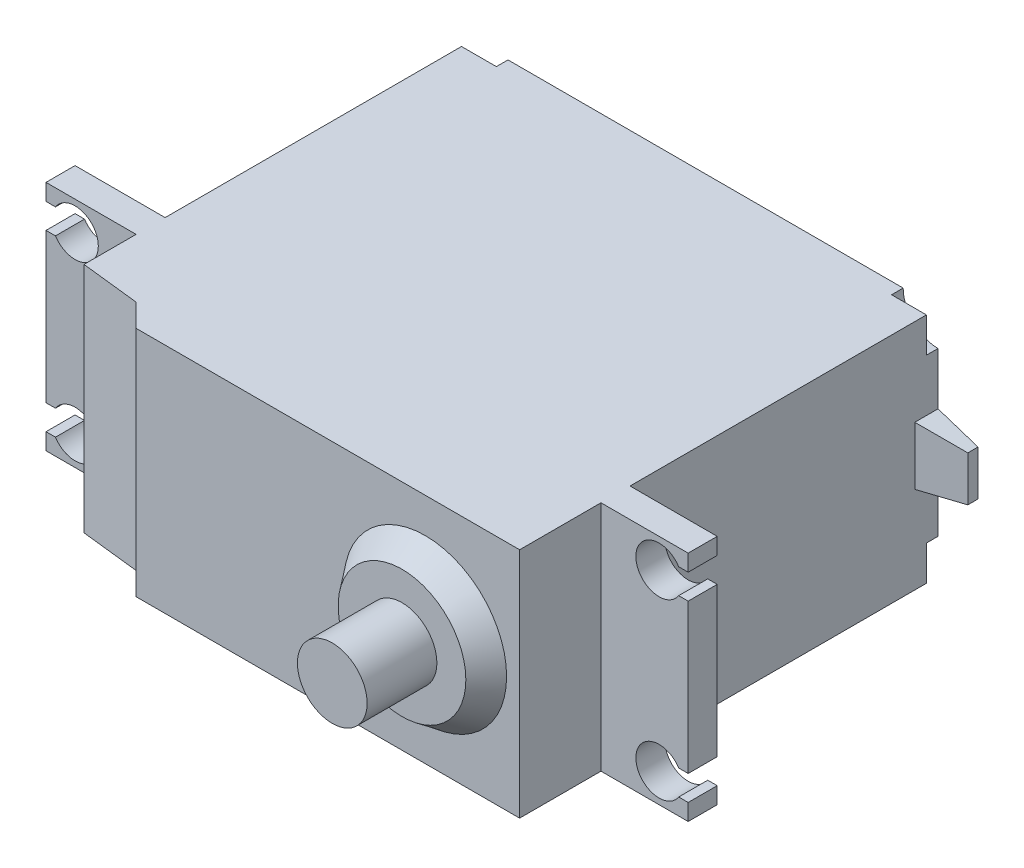
SolidWorks part; units mm, degrees
ref_plane "Front Plane" through (0, 0, 0) normal (0, 0, 1) x (1, 0, 0)
ref_plane "Top Plane" through (0, 0, 0) normal (0, 1, 0) x (1, 0, 0)
ref_plane "Right Plane" through (0, 0, 0) normal (1, 0, 0) x (0, 0, -1)
sketch "Sketch2" plane through (0, 0, 0) normal (0, 0, 1) x (1, 0, 0)
  line L1 (0, 0) -> (40, 0)
  line L2 (0, 0) -> (0, 20)
  line L3 (0, 20) -> (40, 20)
  line L4 (40, 0) -> (40, 20)
  dimension "D1" = 40
  dimension "D2" = 20
extrude "Extrude1" add sketch "Sketch2" along normal blind 36
sketch "Sketch3" plane through (0, 0, 0) normal (-1, 0, 0) x (0, 0, 1)
  line L0 (36, 20) -> (0, 20) construction
  line L1 (26.5, 20) -> (29, 20)
  line L2 (26.5, 20) -> (26.5, 0)
  line L3 (26.5, 0) -> (29, 0)
  line L4 (29, 20) -> (29, 0)
  line L5 (36, 0) -> (0, 0) construction
  line L7 (0, 20) -> (0, 0) construction
  dimension "D1" = 2.5
  dimension "D2" = 26.5
extrude "Extrude2" add sketch "Sketch3" along normal blind 7.75 and the other way blind 47.5
sketch "Sketch4" plane through (0, 0, 0) normal (0, 0, -1) x (-1, 0, 0)
  line L0 (-40, 0) -> (-40, 20) construction
  line L1 (-40, 20) -> (0, 20) construction
  line L2 (-42.3253, 10) -> (1.5611, 10) construction
  line L3 (-20, 21.9817) -> (-20, -2.1649) construction
  line L4 (-37, 20) -> (-40, 20)
  line L5 (-40, 20) -> (-40, 17)
  line L6 (-40, 3) -> (-40, 0)
  line L7 (-40, 0) -> (-37, 0)
  line L8 (0, 3) -> (0, 0)
  line L9 (0, 0) -> (-3, 0)
  line L10 (0, 17) -> (0, 20)
  line L11 (0, 20) -> (-3, 20)
  arc A0 (-40, 17) -> (-37, 20) centre (-40, 20) ccw
  arc A1 (0, 17) -> (-3, 20) centre (0, 20) cw
  arc A2 (0, 3) -> (-3, 0) centre (0, 0) ccw
  arc A3 (-40, 3) -> (-37, 0) centre (-40, 0) cw
  dimension "D1" = 3
extrude "Extrude3" cut sketch "Sketch4" against normal blind 1
sketch "Sketch5" plane through (40, 0, 0) normal (1, 0, 0) x (0, 0, -1)
  line L0 (3.6414, 10) -> (-14.654, 10) construction
  line L1 (0, 7.5) -> (0, 12.5)
  line L2 (0, 3) -> (0, 17) construction
  line L3 (0, 12.5) -> (-2, 12.5)
  line L4 (-2, 12.5) -> (-2, 7.5)
  line L5 (0, 7.5) -> (-2, 7.5)
  point P9 (0, 10)
  point P10 (-2, 10)
  dimension "D1" = 2
  dimension "D2" = 2.5
extrude "Extrude4" add sketch "Sketch5" along normal blind 4 draft 8 separate body
sketch "Sketch6" plane through (0, 0, 29) normal (0, 0, 1) x (1, 0, 0)
  line L0 (0, 20) -> (-7.75, 20) construction
  line L1 (-9.7874, 10) -> (48.9265, 10) construction
  line L2 (20, 22.1) -> (20, -2.1147) construction
  line L3 (-7.75, 0) -> (-7.75, 20) construction
  line L4 (-6.9346, 18.5781) -> (-7.75, 18.5781)
  line L5 (-6.9346, 16.4219) -> (-7.75, 16.4219)
  line L6 (-2.6518, 17.5) -> (-8.5827, 17.5) construction
  line L8 (47.5, 20) -> (40, 20) construction
  line L9 (47.5, 0) -> (47.5, 20) construction
  line L10 (-6.9346, 1.4219) -> (-7.75, 1.4219)
  line L11 (-6.9346, 3.5781) -> (-7.75, 3.5781)
  line L12 (0, 0) -> (40, 0) construction
  line L13 (46.6846, 18.5781) -> (47.5, 18.5781)
  line L14 (44.106, 17.5) -> (48.5714, 17.5) construction
  line L15 (46.6846, 16.4219) -> (47.5, 16.4219)
  line L16 (46.6846, 3.5781) -> (47.5, 3.5781)
  line L17 (46.6846, 1.4219) -> (47.5, 1.4219)
  line L18 (47.5, 3.5781) -> (47.5, 1.4219)
  line L19 (47.5, 1.4219) -> (47.4712, 1.3967)
  line L20 (47.5, 18.5781) -> (47.5, 16.4219)
  line L21 (-7.75, 18.5781) -> (-7.75, 16.4219)
  line L22 (-7.75, 3.5781) -> (-7.75, 1.4219)
  arc A0 (-6.9346, 16.4219) -> (-6.9346, 18.5781) centre (-5.25, 17.5) ccw
  arc A1 (46.6846, 18.5781) -> (46.6846, 16.4219) centre (45, 17.5) ccw
  arc A2 (-6.9346, 3.5781) -> (-6.9346, 1.4219) centre (-5.25, 2.5) cw
  arc A3 (46.6846, 1.4219) -> (46.6846, 3.5781) centre (45, 2.5) cw
  line M3 (-7.75, 20) -> (-7.75, 0)
  dimension "D1" = 4
  dimension "D7" = 4
  dimension "D2" = 2.5
  dimension "D3" = 2.5
  dimension "D4" = 0.8154
  dimension "D5" = 27.75
  dimension "D6" = 10
  dimension "D8" = 2.5
  dimension "D9" = 2.5
  dimension "D10" = 0.8154
extrude "Extrude7" cut sketch "Sketch6" against normal blind 12 and the other way blind 24 contours A2 L11 L10 M3 | L13 A1 L15 L20 | A3 L17 L18 L16 | A0 L4 L21 L5
sketch "Sketch8" plane through (0, 0, 36) normal (0, 0, 1) x (1, 0, 0)
  circle A0 centre (31.8805, 10) radius 7
  dimension "D1" = 14
extrude "Extrude8" add sketch "Sketch8" along normal blind 2 draft 37
sketch "Sketch9" plane through (0, 0, 0) normal (0, -1, 0) x (1, 0, 0)
  line L0 (7, 36) -> (5.0461, 34.0461)
  line L1 (0, 36) -> (40, 36) construction
  line L2 (5.0461, 34.0461) -> (0, 33.4792)
  line L4 (0, 34.0461) -> (0, 36)
  line L5 (0, 36) -> (7, 36)
  line L6 (0, 36) -> (0, 29) construction
  line L7 (0, 33.4792) -> (0, 34.0461)
  dimension "D1" = 7
  dimension "D2" = 141.41
  dimension "D3" = 1.9539
  dimension "D4" = 5.0461
extrude "Extrude9" cut sketch "Sketch9" against normal blind 24 and the other way blind 15
sketch "Sketch10" plane through (0, 0, 38) normal (0, 0, 1) x (1, 0, 0)
  circle A0 centre (31.8805, 10) radius 3
  dimension "D1" = 6
extrude "Extrude10" add sketch "Sketch10" along normal blind 6
